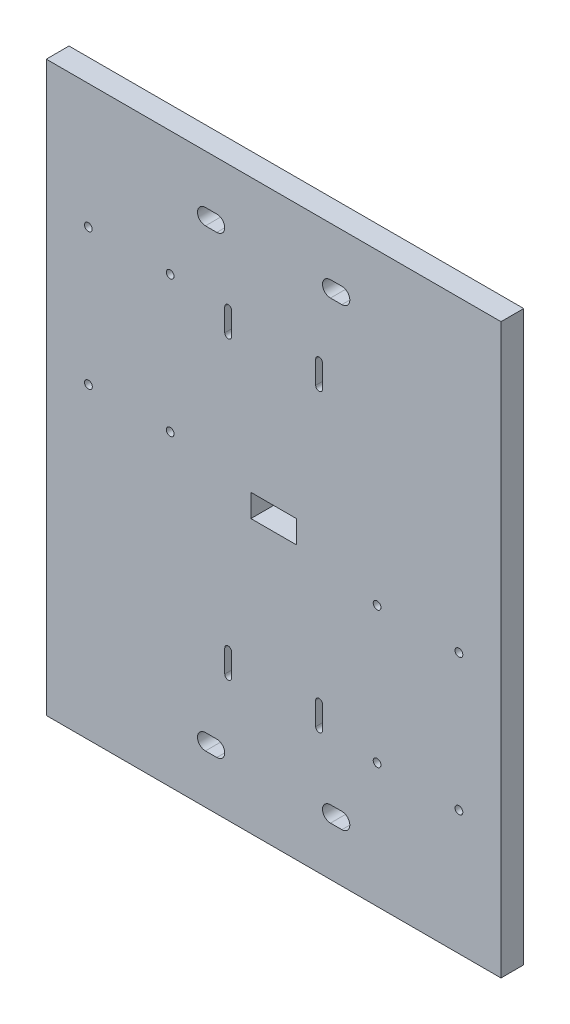
SolidWorks part; units mm, degrees
ref_plane "Plan de face" through (0, 0, 0) normal (0, 0, 1) x (1, 0, 0)
ref_plane "Plan de dessus" through (0, 0, 0) normal (0, 1, 0) x (1, 0, 0)
ref_plane "Plan de droite" through (0, 0, 0) normal (1, 0, 0) x (0, 0, -1)
sketch "Esquisse2" plane through (0, 0, 0) normal (0, 0, 1) x (1, 0, 0)
  line L1 (0, 0) -> (200, 0)
  line L2 (0, 0) -> (0, -250)
  line L3 (0, -250) -> (200, -250)
  line L4 (200, 0) -> (200, -250)
  dimension "D1" = 200
  dimension "D2" = 250
extrude "Boss.-Extru.1" add sketch "Esquisse2" along normal blind 10 contours L1 L4 L3 L2
sketch "Esquisse7" plane through (0, 0, 0) normal (0, 0, -1) x (-1, 0, 0)
  line L0 (0, 0) -> (-200, 0) construction
  line L1 (-110, -130) -> (-90, -130)
  line L2 (-110, -130) -> (-110, -120)
  line L3 (-110, -120) -> (-90, -120)
  line L4 (-90, -130) -> (-90, -120)
  line L6 (-200, 0) -> (-200, -250) construction
  line L7 (0, 0) -> (0, -250) construction
  line L8 (0, -250) -> (-200, -250) construction
  dimension "D1" = 10
  dimension "D2" = 120
  dimension "D3" = 90
  dimension "D4" = 90
extrude "Enlèv. mat.-Extru.2" cut sketch "Esquisse7" against normal blind 10
sketch "Esquisse9" plane through (0, 0, 10) normal (0, 0, 1) x (1, 0, 0)
  line L0 (0, 0) -> (0, -250) construction
  line L1 (200, 0) -> (200, -250) construction
  circle A0 centre (5, -50.3051) radius 3
  circle A1 centre (195, -50.3051) radius 3
  dimension "D1" = 6
  dimension "D2" = 6
  dimension "D3" = 5
  dimension "D4" = 5
extrude "Boss.-Extru.2" [suppressed] add sketch "Esquisse9" along normal blind 6
fillet "Congé3" [suppressed] radius 2
sketch "Esquisse10" plane through (0, 0, 0) normal (0, 0, -1) x (-1, 0, 0)
  line L0 (-70, -25) -> (-75, -25) construction
  line L1 (-70, -28.5) -> (-75, -28.5)
  line L2 (-70, -21.5) -> (-75, -21.5)
  line L3 (-70, -225) -> (-75, -225) construction
  line L4 (-70, -228.5) -> (-75, -228.5)
  line L5 (-70, -221.5) -> (-75, -221.5)
  line L6 (-130, -225) -> (-125, -225) construction
  line L7 (-130, -221.5) -> (-125, -221.5)
  line L8 (-130, -228.5) -> (-125, -228.5)
  line L9 (-130, -25) -> (-125, -25) construction
  line L10 (-130, -21.5) -> (-125, -21.5)
  line L11 (-130, -28.5) -> (-125, -28.5)
  line L12 (0, 0) -> (-200, 0) construction
  line L14 (0, -250) -> (-200, -250) construction
  line L16 (-127.5, 0) -> (-127.5, -250) construction
  line L17 (-72.5, 0) -> (-72.5, -250) construction
  line L21 (-110, -120) -> (-110, -130) construction
  line L22 (-90, -130) -> (-90, -120) construction
  line L24 (-200, 0) -> (-200, -250) construction
  arc A0 (-70, -28.5) -> (-70, -21.5) centre (-70, -25) ccw
  arc A1 (-75, -21.5) -> (-75, -28.5) centre (-75, -25) ccw
  arc A2 (-70, -228.5) -> (-70, -221.5) centre (-70, -225) ccw
  arc A3 (-75, -221.5) -> (-75, -228.5) centre (-75, -225) ccw
  arc A4 (-130, -221.5) -> (-130, -228.5) centre (-130, -225) ccw
  arc A5 (-125, -228.5) -> (-125, -221.5) centre (-125, -225) ccw
  arc A6 (-130, -21.5) -> (-130, -28.5) centre (-130, -25) ccw
  arc A7 (-125, -28.5) -> (-125, -21.5) centre (-125, -25) ccw
  point P2 (-72.5, -25)
  point P7 (-72.5, -225)
  point P14 (-127.5, -225)
  point P21 (-127.5, -25)
  point P36 (-121.5, -225)
  point P37 (-78.5, -225)
  point P38 (-133.5, -225)
  point P41 (-110, -125)
  point P44 (-90, -125)
  point P45 (-66.5, -225)
  point P46 (-121.5, -25)
  point P47 (-78.5, -25)
  dimension "D2" = 43
  dimension "D3" = 5
  dimension "D4" = 7
  dimension "D5" = 7
  dimension "D6" = 0
  dimension "D7" = 100
  dimension "D8" = 72.5
  dimension "D9" = 5
  dimension "D10" = 7
  dimension "D11" = 100
  dimension "D12" = 0
  dimension "D13" = 7
  dimension "D14" = 5
  dimension "D15" = 100
  dimension "D16" = 0
  dimension "D17" = 0
  dimension "D18" = 100
  dimension "D19" = 5
extrude "Enlèv. mat.-Extru.3" cut sketch "Esquisse10" against normal blind 10
sketch "Esquisse11" plane through (0, 0, 0) normal (0, 0, -1) x (-1, 0, 0)
  line L2 (-80, -55) -> (-80, -65) construction
  line L4 (-90, -120) -> (-110, -120) construction
  line L6 (-78.5, -55) -> (-78.5, -65)
  line L7 (-81.5, -55) -> (-81.5, -65)
  line L8 (0, 0) -> (0, -250) construction
  line L9 (-120, -55) -> (-120, -65) construction
  line L10 (-118.5, -55) -> (-118.5, -65)
  line L11 (-121.5, -55) -> (-121.5, -65)
  line L12 (-200, 0) -> (-200, -250) construction
  line L13 (-120, -195) -> (-120, -185) construction
  line L14 (-121.5, -195) -> (-121.5, -185)
  line L15 (-118.5, -195) -> (-118.5, -185)
  line L16 (-110, -130) -> (-90, -130) construction
  line L17 (-80, -195) -> (-80, -185) construction
  line L18 (-81.5, -195) -> (-81.5, -185)
  line L19 (-78.5, -195) -> (-78.5, -185)
  arc A6 (-78.5, -55) -> (-81.5, -55) centre (-80, -55) ccw
  arc A7 (-81.5, -65) -> (-78.5, -65) centre (-80, -65) ccw
  arc A8 (-118.5, -55) -> (-121.5, -55) centre (-120, -55) ccw
  arc A9 (-121.5, -65) -> (-118.5, -65) centre (-120, -65) ccw
  arc A10 (-121.5, -195) -> (-118.5, -195) centre (-120, -195) ccw
  arc A11 (-118.5, -185) -> (-121.5, -185) centre (-120, -185) ccw
  arc A12 (-81.5, -195) -> (-78.5, -195) centre (-80, -195) ccw
  arc A13 (-78.5, -185) -> (-81.5, -185) centre (-80, -185) ccw
  point P0 (-80, -190)
  point P2 (-120, -190)
  point P4 (-80, -60)
  point P6 (-120, -60)
  point P12 (-120, -60)
  point P14 (-80, -60)
  point P28 (-120, -190)
  point P36 (-80, -190)
  dimension "D3" = 10
  dimension "D4" = 3
  dimension "D5" = 10
  dimension "D9" = 60
  dimension "D10" = 80
  dimension "D2" = 10
  dimension "D6" = 3
  dimension "D7" = 3
  dimension "D8" = 10
  dimension "D11" = 60
  dimension "D12" = 80
  dimension "D13" = 60
  dimension "D14" = 80
  dimension "D15" = 3
  dimension "D16" = 80
  dimension "D17" = 60
extrude "Enlèv. mat.-Extru.4" cut sketch "Esquisse11" against normal blind 10
sketch "Esquisse12" plane through (0, 0, 0) normal (0, 0, -1) x (-1, 0, 0)
  line L0 (-121.5, -190) -> (0, -190) construction
  line L1 (-121.5, -185) -> (-121.5, -195) construction
  line L2 (0, 0) -> (0, -250) construction
  line L3 (0, -190) -> (-200, -190) construction
  line L4 (-118.5, -60) -> (0, -60) construction
  line L5 (0, 0) -> (0, -250) construction
  line L6 (0, -54.7) -> (-200, -54.7) construction
  line L7 (-200, 0) -> (-200, -250) construction
  line L8 (-200, 0) -> (-200, -250) construction
  line L9 (-118.5, -65) -> (-118.5, -55) construction
  line L11 (0, -191.5) -> (0, -195.3) construction
  line L12 (0, -195.3) -> (-200, -195.3) construction
  point P15 (-54.5, -54.7)
  point P19 (-18.5, -54.7)
  point P21 (-54.5, -114.7)
  point P22 (-18.5459, -114.7)
  point P24 (-200, -190)
  point P25 (0, -60)
  point P29 (-145.5, -195.3)
  point P34 (-181.5, -195.3)
  point P35 (-181.5, -135.3)
  point P36 (-145.5, -135.3)
  dimension "D2" = 18.5
  dimension "D6" = 18.5
  dimension "D3" = 36
  dimension "D4" = 60
  dimension "D7" = 36
  dimension "D8" = 60
  dimension "D9" = 36
sketch "Esquisse13" plane through (0, 0, 0) normal (0, 0, -1) x (-1, 0, 0)
  line L0 (-130, -28.5) -> (-125, -28.5) construction
  line L1 (-133.55, -228.55) -> (-121.45, -228.55)
  line L2 (-133.55, -228.55) -> (-133.55, -221.45)
  line L3 (-133.55, -221.45) -> (-121.45, -221.45)
  line L4 (-121.45, -228.55) -> (-121.45, -221.45)
  line L5 (-78.55, -228.55) -> (-66.45, -228.55)
  line L6 (-78.55, -228.55) -> (-78.55, -221.45)
  line L7 (-78.55, -221.45) -> (-66.45, -221.45)
  line L8 (-66.45, -228.55) -> (-66.45, -221.45)
  line L9 (-133.55, -28.55) -> (-121.45, -28.55)
  line L10 (-133.55, -28.55) -> (-133.55, -21.45)
  line L11 (-133.55, -21.45) -> (-121.45, -21.45)
  line L12 (-121.45, -28.55) -> (-121.45, -21.45)
  line L13 (-78.55, -28.55) -> (-66.45, -28.55)
  line L14 (-78.55, -28.55) -> (-78.55, -21.45)
  line L15 (-78.55, -21.45) -> (-66.45, -21.45)
  line L16 (-66.45, -28.55) -> (-66.45, -21.45)
  line L17 (-75, -28.5) -> (-70, -28.5) construction
  line L18 (-75, -228.5) -> (-70, -228.5) construction
  line L19 (-130, -228.5) -> (-125, -228.5) construction
  arc A0 (-130, -21.5) -> (-130, -28.5) centre (-130, -25) ccw construction
  arc A1 (-75, -21.5) -> (-75, -28.5) centre (-75, -25) ccw construction
  arc A2 (-75, -221.5) -> (-75, -228.5) centre (-75, -225) ccw construction
  arc A3 (-130, -221.5) -> (-130, -228.5) centre (-130, -225) ccw construction
  point P21 (-133.5, -25)
  point P25 (-78.5, -25)
  point P31 (-78.5, -225)
  point P39 (-133.5, -225)
  dimension "D1" = 12.1
  dimension "D2" = 7.1
  dimension "D3" = 0.05
  dimension "D4" = 0.05
  dimension "D5" = 7.1
  dimension "D6" = 12.1
  dimension "D7" = 0.05
  dimension "D8" = 0.05
  dimension "D9" = 12.1
  dimension "D10" = 7.1
  dimension "D11" = 0.05
  dimension "D12" = 0.05
  dimension "D13" = 12.1
  dimension "D14" = 7.1
  dimension "D15" = 0.05
  dimension "D16" = 0.05
split line "Ligne de séparation1"
hole_wizard "Dégagement M31" positions "Esquisse15" profile "Esquisse16" hole size "M3" standard "ISO" end condition through all
sketch "Esquisse15" plane through (0, 0, 10) normal (0, 0, 1) x (1, 0, 0)
  point P0 (18.5, -54.7)
  point P3 (54.5, -54.7)
  point P6 (18.5459, -114.7)
  point P9 (54.5, -114.7)
  point P12 (145.5, -135.3)
  point P15 (181.5, -135.3)
  point P18 (145.5, -195.3)
  point P21 (181.5, -195.3)
sketch "Esquisse16" plane through (18.5, -54.7, 10) normal (1, 0, 0) x (0, -1, 0)
  line L0 (0, 0) -> (0, 10)
  line L1 (0, 10) -> (1.7, 10)
  line L2 (1.7, 10) -> (1.7, 0)
  line L5 (1.7, 0) -> (0, 0)
  line L11 (0, -6.35) -> (0, 107.95) construction
  dimension "Diamètre du perçage jusqu'au prochain" = 3.4
  dimension "Profondeur du perçage jusqu'au prochain" = 10
